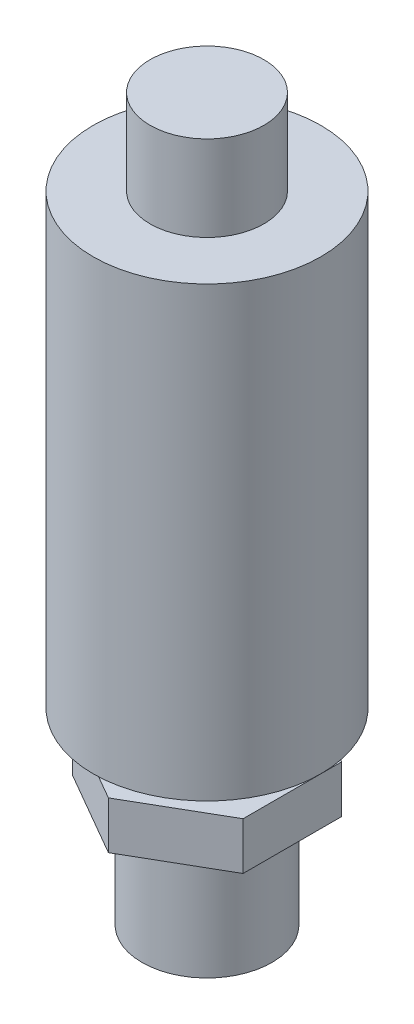
SolidWorks part; units mm, degrees
ref_plane "Front Plane" through (0, 0, 0) normal (0, 0, 1) x (1, 0, 0)
ref_plane "Top Plane" through (0, 0, 0) normal (0, 1, 0) x (1, 0, 0)
ref_plane "Right Plane" through (0, 0, 0) normal (1, 0, 0) x (0, 0, -1)
sketch "Sketch1" plane through (0, 0, 0) normal (0, 1, 0) x (1, 0, 0)
  circle A0 centre (0, 0) radius 6.85
  dimension "D1" = 13.7
extrude "Boss-Extrude1" add sketch "Sketch1" along normal blind 11.8
sketch "Sketch2" plane through (0, 11.8, 0) normal (0, 1, 0) x (1, 0, 0)
  line L1 (0, 10.3923) -> (-9, 5.1962)
  line L2 (-9, 5.1962) -> (-9, -5.1962)
  line L3 (-9, -5.1962) -> (0, -10.3923)
  line L4 (0, -10.3923) -> (9, -5.1962)
  line L5 (9, -5.1962) -> (9, 5.1962)
  line L6 (9, 5.1962) -> (0, 10.3923)
  circle A0 centre (0, 0) radius 9 construction
extrude "Boss-Extrude2" add sketch "Sketch2" along normal blind 5
sketch "Sketch3" plane through (0, 16.8, 0) normal (0, 1, 0) x (1, 0, 0)
  circle A0 centre (0, 0) radius 5
  dimension "D1" = 10
extrude "Boss-Extrude3" add sketch "Sketch3" along normal blind 3
sketch "Sketch4" plane through (0, 19.8, 0) normal (0, 1, 0) x (1, 0, 0)
  circle A0 centre (0, 0) radius 12
  dimension "D1" = 24
extrude "Boss-Extrude4" add sketch "Sketch4" along normal blind 47.2
sketch "Sketch5" plane through (0, 67, 0) normal (0, 1, 0) x (1, 0, 0)
  circle A0 centre (0, 0) radius 6
  dimension "D1" = 12
extrude "Boss-Extrude5" add sketch "Sketch5" along normal blind 9
